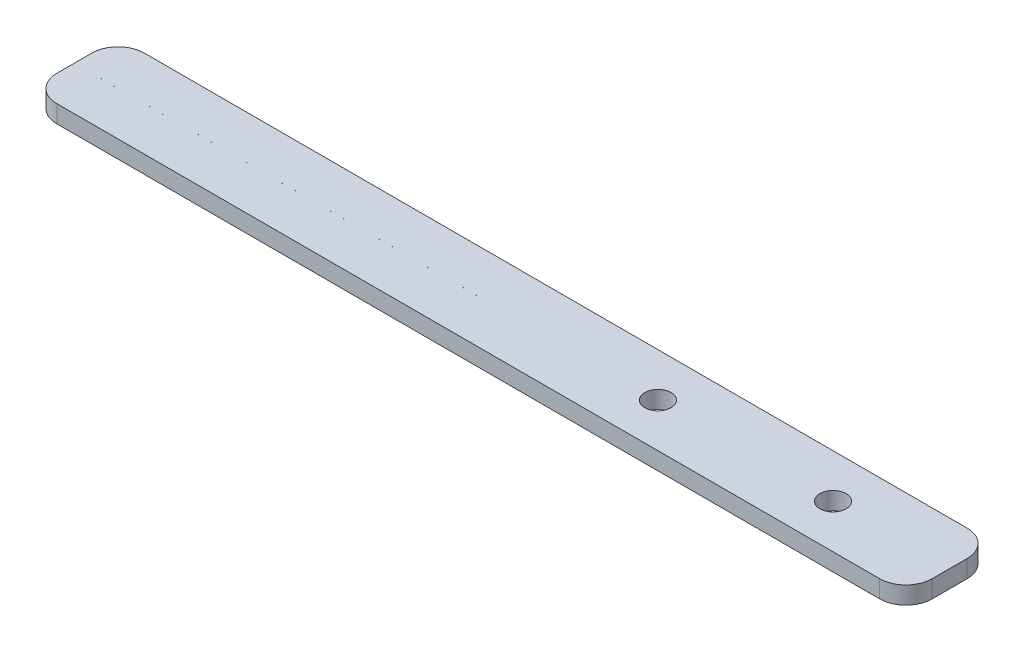
SolidWorks part; units mm, degrees
ref_plane "Front Plane" through (0, 0, 0) normal (0, 0, 1) x (1, 0, 0)
ref_plane "Top Plane" through (0, 0, 0) normal (0, 1, 0) x (1, 0, 0)
ref_plane "Right Plane" through (0, 0, 0) normal (1, 0, 0) x (0, 0, -1)
sketch "Sketch1" plane through (0, 0, 0) normal (0, 1, 0) x (1, 0, 0)
  line L1 (-50, 5) -> (50, 5)
  line L2 (-50, 5) -> (-50, -5)
  line L3 (-50, -5) -> (50, -5)
  line L4 (50, 5) -> (50, -5)
  line L5 (-50, 5) -> (50, -5) construction
  line L6 (-50, -5) -> (50, 5) construction
  point P0 (0, 0)
  dimension "D1" = 10
  dimension "D2" = 100
extrude "Boss-Extrude1" add sketch "Sketch1" along normal blind 2
sketch "Sketch2" plane through (0, 2, 0) normal (0, 1, 0) x (1, 0, 0)
  line L0 (26.3156, 5) -> (26.3156, -5) construction
  line L1 (-50, -5) -> (50, -5) construction
  line L2 (-50, 5) -> (-50, -5) construction
  line L4 (-3, 0.0005) -> (-50, 0.0005)
  line L5 (-3, 0.0005) -> (-3, -0.0005)
  line L6 (-3, -0.0005) -> (-50, -0.0005)
  line L7 (-50, 0.0005) -> (-50, -0.0005)
  line L8 (-3, 0.0005) -> (-50, -0.0005) construction
  line L9 (-3, -0.0005) -> (-50, 0.0005) construction
  point P0 (-26.5, 0)
  point P10 (26.3156, 0)
  point P13 (0, 0)
  point P14 (-50, 0)
  dimension "D1" = 47
  dimension "D2" = 0.001
fillet "Fillet1" radius 3 4 edges at (50, 1, 5) (50, 1, -5) (-50, 1, -5) (-50, 1, 5)
hole_wizard "Ø3.0mm Dowel Hole1" positions "Sketch3" profile "Sketch5" hole size "Ø3.0" standard "ISO" end condition through all
sketch "Sketch3" plane through (0, 2, 0) normal (0, 1, 0) x (1, 0, 0)
  point P0 (36.6695, 0)
  point P5 (16.6695, 0)
  dimension "D1" = 20
sketch "Sketch5" plane through (36.6695, 2, 0) normal (1, 0, 0) x (0, 0, 1)
  line L0 (0, 0) -> (0, 2)
  line L1 (0, 2) -> (1.5, 2)
  line L2 (1.5, 2) -> (1.5, 0)
  line L5 (1.5, 0) -> (0, 0)
  line L11 (0, -22.0399) -> (0, 107.95) construction
  dimension "Thru Hole Dia." = 3
  dimension "Thru Hole Depth" = 2
extrude "Cut-Extrude1" cut sketch "Sketch2" against normal blind 10
